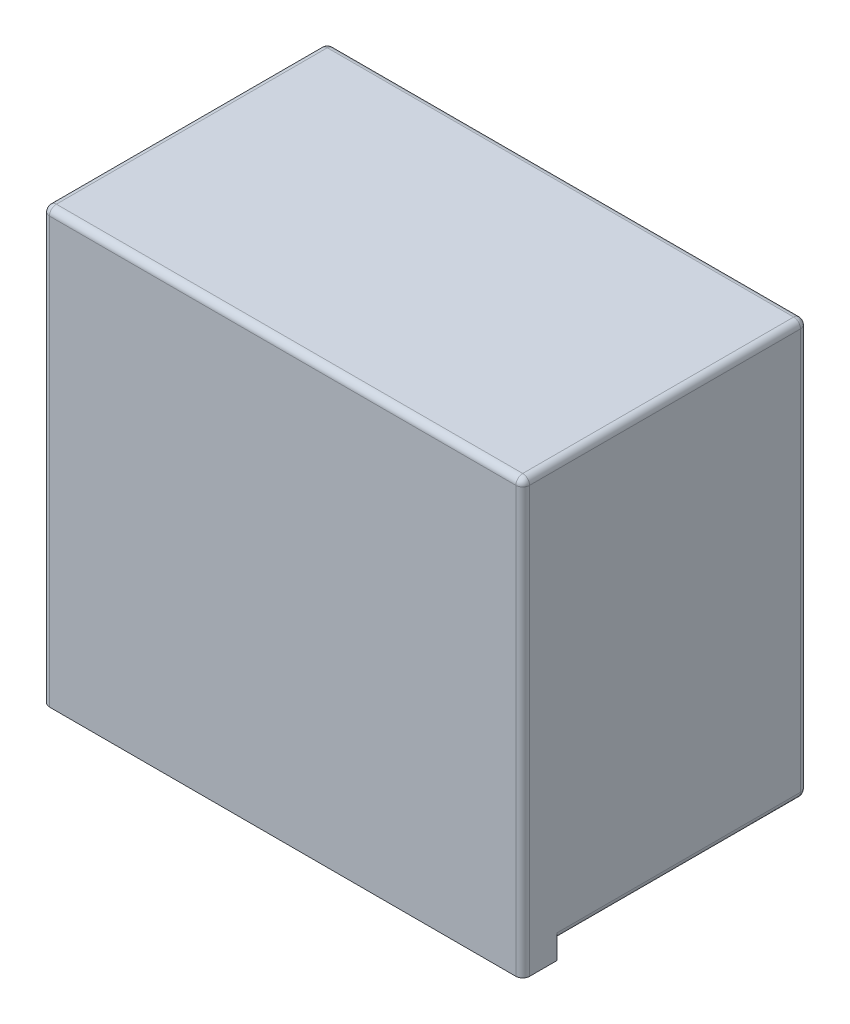
SolidWorks part; units mm, degrees
ref_plane "Front Plane" through (0, 0, 0) normal (0, 0, 1) x (1, 0, 0)
ref_plane "Top Plane" through (0, 0, 0) normal (0, 1, 0) x (1, 0, 0)
ref_plane "Right Plane" through (0, 0, 0) normal (1, 0, 0) x (0, 0, -1)
sketch "Sketch1" plane through (0, 0, 0) normal (0, 0, 1) x (1, 0, 0)
  line L1 (0, 0) -> (14, 0)
  line L2 (0, 0) -> (0, 12.6)
  line L3 (0, 12.6) -> (14, 12.6)
  line L4 (14, 0) -> (14, 12.6)
  dimension "D1" = 14
  dimension "D2" = 12.6
extrude "Extrude1" add sketch "Sketch1" along normal blind 8.3
sketch "Sketch2" plane through (0, 0, 0) normal (0, 0, -1) x (-1, 0, 0)
  line L0 (-14.677, 10.9) -> (-1.1655, 10.9) construction
  line L1 (-14, 12.6) -> (0, 12.6) construction
  line L2 (-7, 0) -> (-7, -0.6221) construction
  line L3 (0, 0) -> (-14, 0) construction
  circle A0 centre (-7, 6.15) radius 4.75
  dimension "D1" = 9.5
  dimension "D2" = 1.7
extrude "Cut-Extrude1" cut sketch "Sketch2" against normal blind 7.3
fillet "Fillet1" radius 0.5 1 edges at (2.25, 6.15, 0)
sketch "Sketch3" plane through (0, 0, 0) normal (0, 0, -1) x (-1, 0, 0)
  line L0 (-7, 1.4) -> (-4.2619, 1.4) construction
  line L2 (-14, 0) -> (-14, 12.6) construction
  line L3 (-11.6, 0.5) -> (-2.4, 0.5)
  line L4 (-11.6, 0.5) -> (-11.6, -0.2894)
  line L5 (-11.6, -0.2894) -> (-2.4, -0.2894)
  line L6 (-2.4, 0.5) -> (-2.4, -0.2894)
  line L7 (-1, 0.5) -> (1.0352, 0.5)
  line L8 (-1, 0.5) -> (-1, -0.2894)
  line L9 (-1, -0.2894) -> (1.0352, -0.2894)
  line L10 (1.0352, 0.5) -> (1.0352, -0.2894)
  line L11 (-14.7281, 0.5) -> (-13, 0.5)
  line L12 (-14.7281, 0.5) -> (-14.7281, -0.6477)
  line L13 (-14.7281, -0.6477) -> (-13, -0.6477)
  line L14 (-13, 0.5) -> (-13, -0.6477)
  line L15 (0, 12.6) -> (0, 0) construction
  line L16 (0, 0) -> (-14, 0) construction
  circle A2 centre (-7, 6.15) radius 4.75 construction
  circle A3 centre (-7, 6.15) radius 4.75 construction
  dimension "D1" = 1.4
  dimension "D2" = 1
  dimension "D3" = 1
  dimension "D4" = 1.4
  dimension "D5" = 0.5
extrude "Cut-Extrude2" cut sketch "Sketch3" against normal blind 7.3
fillet "Fillet2" radius 0.5 2 edges at (1.7, 0, 0) (12.3, 0, 0)
sketch "Sketch4" plane through (0, 0, 0) normal (0, 0, -1) x (-1, 0, 0)
  line L0 (-7, 2.3) -> (-2.1635, 2.3) construction
  line L1 (-10.5242, 4.6) -> (-9.35, 4.6)
  line L4 (-9.35, 4.6) -> (-9.35, 3.1004)
  line L5 (-7, 10) -> (-7, 10.5095) construction
  line L6 (-4.65, 4.6) -> (-4.65, 3.1004)
  line L9 (-3.4758, 4.6) -> (-4.65, 4.6)
  line L12 (-7.9, 9.8933) -> (-7.9, 9.3)
  line L13 (-7.9, 9.3) -> (-6.1, 9.3)
  line L14 (-6.1, 9.8933) -> (-6.1, 9.3)
  arc A0 (-3.4758, 4.6) -> (-6.1, 9.8933) centre (-7, 6.15) ccw
  arc A1 (-9.35, 3.1004) -> (-4.65, 3.1004) centre (-7, 6.15) ccw
  arc A2 (-7.9, 9.8933) -> (-10.5242, 4.6) centre (-7, 6.15) ccw
  dimension "D1" = 7.7
  dimension "D2" = 2.35
  dimension "D3" = 2.3
  dimension "D4" = 4.7
  dimension "D6" = 0.9
extrude "Extrude2" add sketch "Sketch4" against normal up to surface (7.3 mm away) separate body up to face at (2.25, 6.15, 7.3)
sketch "Sketch5" plane through (0, 0, 0) normal (0, 0, -1) x (-1, 0, 0)
  line L0 (-6.1, 9.3) -> (-7.9, 9.3) construction
  line L1 (-7.75, 8.5) -> (-6.25, 8.5)
  line L2 (-7.75, 8.5) -> (-7.75, 6.3)
  line L3 (-7.75, 6.3) -> (-6.25, 6.3)
  line L4 (-6.25, 8.5) -> (-6.25, 6.3)
  line L6 (-6.25, 8.5) -> (-6.25, 6.3)
  circle A0 centre (-8.2283, 3.7538) radius 0.3
  circle A1 centre (-9.7381, 5.7754) radius 0.3
  circle A2 centre (-9.3287, 8.0017) radius 0.3
  circle A3 centre (-4.6713, 8.0017) radius 0.3
  circle A4 centre (-4.2619, 5.7754) radius 0.3
  circle A5 centre (-5.7717, 3.7538) radius 0.3
  dimension "D5" = 0.6
  dimension "D6" = 0.6
  dimension "D7" = 0.6
  dimension "D1" = 0.8
  dimension "D2" = 2.2
  dimension "D3" = 1.5
extrude "Cut-Extrude3" cut sketch "Sketch5" against normal blind 7.3 contours L4 L1 L2 L3 | A3 | A4 | A2 | A1 | A0 | A5
chamfer "Chamfer1" distance 0.4 angle 45 6 edges at (3.9619, 5.7754, 0) (4.3713, 8.0017, 0) (9.0287, 8.0017, 0) (9.4381, 5.7754, 0) (5.4717, 3.7538, 0) (7.9283, 3.7538, 0)
fillet "Fillet3" radius 0.2 13 edges at (0.5, 0.5, 0) (7, 0.5, 0) (14, 0.5, 3.65) (0, 0.5, 3.65) (13.5, 0.5, 0) (0, 6.3, 8.3) (0, 12.6, 4.15) (7, 12.6, 8.3) (14, 6.3, 8.3) (14, 12.6, 4.15) (0, 6.55, 0) (14, 6.55, 0) (7, 12.6, 0)
